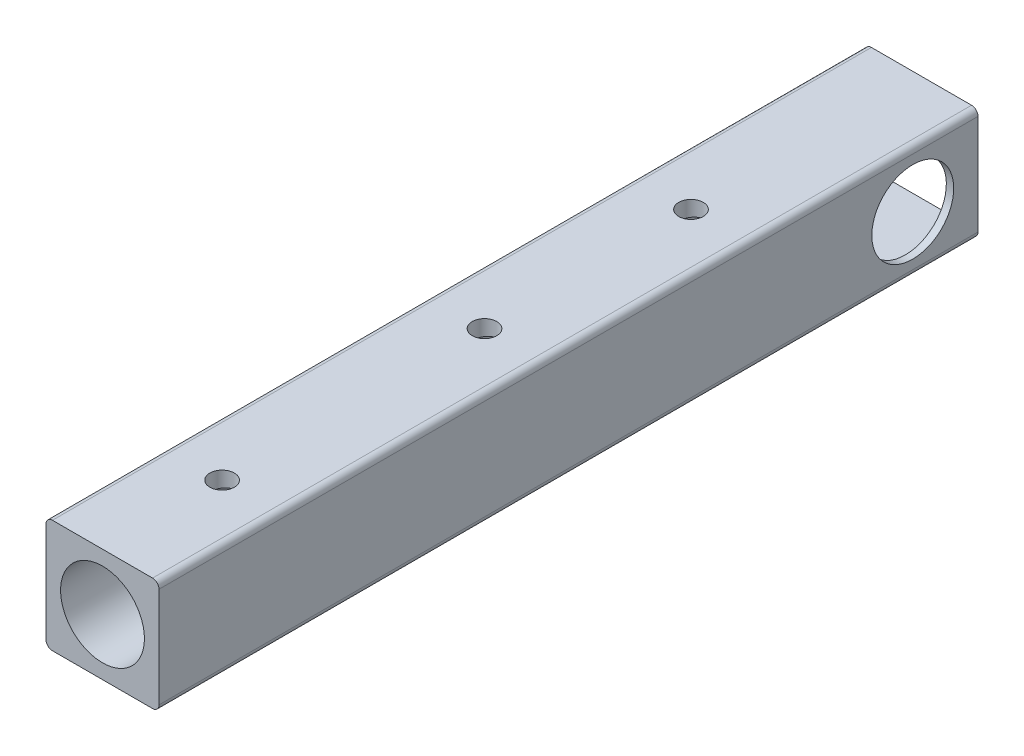
SolidWorks part; units mm, degrees
ref_plane "Front Plane" through (0, 0, 0) normal (0, 0, 1) x (1, 0, 0)
ref_plane "Top Plane" through (0, 0, 0) normal (0, 1, 0) x (1, 0, 0)
ref_plane "Right Plane" through (0, 0, 0) normal (1, 0, 0) x (0, 0, -1)
sketch "Sketch1" plane through (0, 0, 0) normal (0, 0, 1) x (1, 0, 0)
  line L1 (-15.24, 15.24) -> (15.24, 15.24)
  line L2 (-15.24, 15.24) -> (-15.24, -15.24)
  line L3 (-15.24, -15.24) -> (15.24, -15.24)
  line L4 (15.24, 15.24) -> (15.24, -15.24)
  line L5 (-15.24, 15.24) -> (15.24, -15.24) construction
  line L6 (-15.24, -15.24) -> (15.24, 15.24) construction
  line L7 (-17.526, 17.526) -> (17.526, 17.526)
  line L8 (-17.526, 17.526) -> (-17.526, -17.526)
  line L9 (-17.526, -17.526) -> (17.526, -17.526)
  line L10 (17.526, 17.526) -> (17.526, -17.526)
  line L11 (-17.526, 17.526) -> (17.526, -17.526) construction
  line L12 (-17.526, -17.526) -> (17.526, 17.526) construction
  point P0 (0, 0)
  point P5 (0, 0)
  dimension "D1" = 30.48
  dimension "D2" = 30.48
  dimension "D3" = 35.052
  dimension "D4" = 35.052
extrude "Boss-Extrude1" add sketch "Sketch1" along normal blind 254
fillet "Fillet1" radius 2 4 edges at (-17.526, -17.526, 127) (17.526, -17.526, 127) (-17.526, 17.526, 127) (17.526, 17.526, 127)
fillet "Fillet2" radius 2 4 edges at (15.24, 15.24, 127) (-15.24, 15.24, 127) (-15.24, -15.24, 127) (15.24, -15.24, 127)
sketch "Sketch2" plane through (-17.526, 0, 0) normal (-1, 0, 0) x (0, 0, 1)
  circle A0 centre (20.2344, 0) radius 12.7
extrude "Cut-Extrude1" cut sketch "Sketch2" against normal blind 254
sketch "Sketch3" plane through (0, 17.526, 0) normal (0, 1, 0) x (1, 0, 0)
  circle A0 centre (0, -135.5272) radius 3.81
  circle A1 centre (0, -216.9107) radius 3.81
  circle A2 centre (0, -71.4908) radius 3.81
extrude "Cut-Extrude2" cut sketch "Sketch3" against normal blind 254
sketch "Sketch4" plane through (0, 17.526, 0) normal (0, 1, 0) x (1, 0, 0)
  line L0 (-15.526, 0) -> (-15.526, -254) construction
  line L1 (-15.526, -45.132) -> (15.526, -45.132)
  line L2 (-15.526, -45.132) -> (-15.526, -39.6696)
  line L3 (-15.526, -39.6696) -> (15.526, -39.6696)
  line L4 (15.526, -45.132) -> (15.526, -39.6696)
  line L5 (15.526, -254) -> (15.526, 0) construction
extrude "Boss-Extrude3" add sketch "Sketch4" against normal up to body
sketch "Sketch6" plane through (0, 0, 254) normal (0, 0, 1) x (1, 0, 0)
  line L0 (15.24, -13.24) -> (15.24, 13.24) construction
  line L1 (-15.24, 15.24) -> (15.24, 15.24)
  line L2 (-15.24, 15.24) -> (-15.24, -15.24)
  line L3 (-15.24, -15.24) -> (15.24, -15.24)
  line L4 (15.24, 15.24) -> (15.24, -15.24)
  line L5 (-15.24, 15.24) -> (15.24, -15.24) construction
  line L6 (-15.24, -15.24) -> (15.24, 15.24) construction
  line L7 (13.24, 15.24) -> (-13.24, 15.24) construction
  circle A0 centre (0, 0) radius 13
extrude "Boss-Extrude4" add sketch "Sketch6" against normal blind 217.402
sketch "Sketch7" plane through (0, 17.526, 0) normal (0, 1, 0) x (1, 0, 0)
  circle A0 centre (0, -71.4908) radius 3.81 construction
  circle A1 centre (0, -71.4908) radius 3.81
  circle A2 centre (0, -135.5272) radius 3.81 construction
  circle A3 centre (0, -135.5272) radius 3.81
  circle A4 centre (0, -216.9107) radius 3.81 construction
  circle A5 centre (0, -216.9107) radius 3.81
extrude "Cut-Extrude3" cut sketch "Sketch7" against normal blind 217.402
